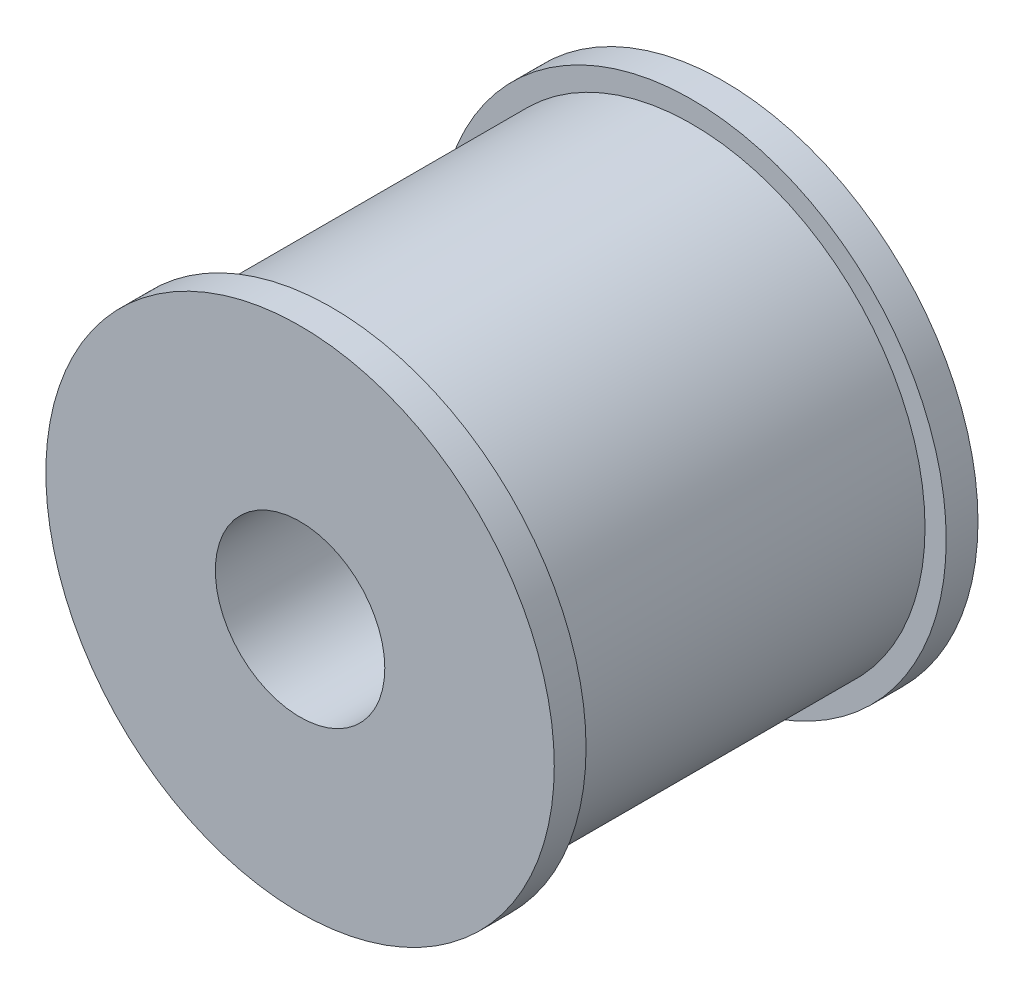
SolidWorks part; units mm, degrees
material "Manganese Bronze"
ref_plane "Front Plane" through (0, 0, 0) normal (0, 0, 1) x (1, 0, 0)
ref_plane "Top Plane" through (0, 0, 0) normal (0, 1, 0) x (1, 0, 0)
ref_plane "Right Plane" through (0, 0, 0) normal (1, 0, 0) x (0, 0, -1)
sketch "Sketch1" plane through (0, 0, 0) normal (0, 0, 1) x (1, 0, 0)
  circle A0 centre (0, 0) radius 12
  circle A1 centre (0, 0) radius 4
extrude "Boss-Extrude1" add sketch "Sketch1" along normal blind 20
sketch "Sketch2" plane through (0, 0, 20) normal (0, 0, 1) x (1, 0, 0)
  circle A0 centre (0, 0) radius 11
  circle A1 centre (0, 0) radius 17.9112
extrude "Cut-Extrude1" cut sketch "Sketch2" against normal blind 17 from offset 1.5 offset against normal yes
